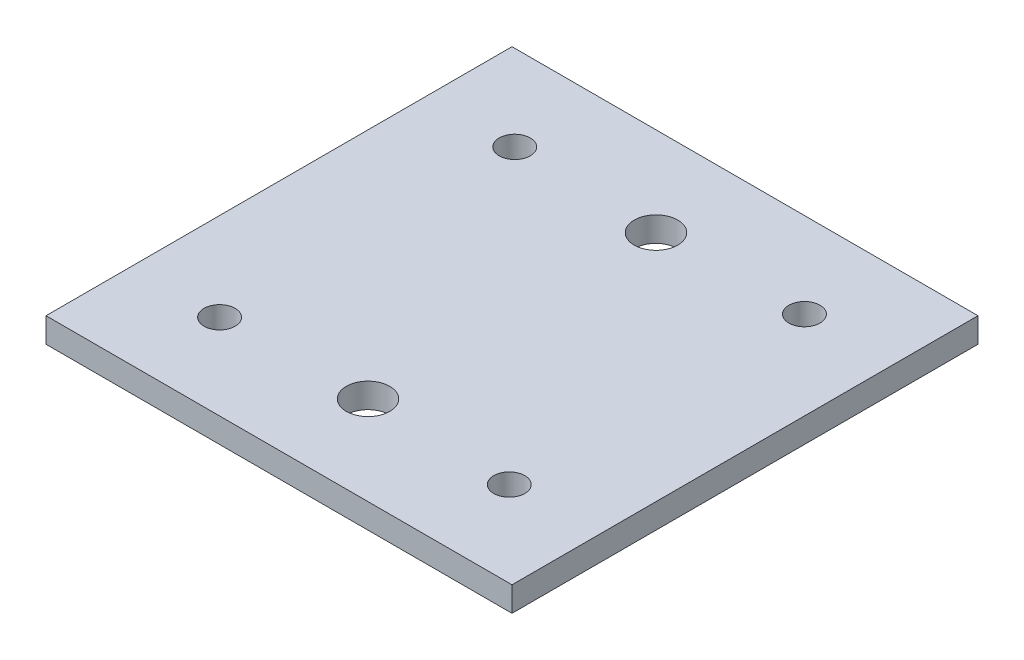
SolidWorks part; units mm, degrees
ref_plane "Front Plane" through (0, 0, 0) normal (0, 0, 1) x (1, 0, 0)
ref_plane "Top Plane" through (0, 0, 0) normal (0, 1, 0) x (1, 0, 0)
ref_plane "Right Plane" through (0, 0, 0) normal (1, 0, 0) x (0, 0, -1)
sketch "Sketch1" plane through (0, 0, 0) normal (1, 0, 0) x (0, 0, -1)
  line L1 (0, 0) -> (150, 0)
  line L2 (0, 0) -> (0, -7.9622)
  line L3 (0, -7.9622) -> (150, -7.9622)
  line L4 (150, 0) -> (150, -7.9622)
  dimension "D1" = 150
extrude "Boss-Extrude1" add sketch "Sketch1" along normal blind 150 contours L3 L4 L1 L2
sketch "Sketch2" plane through (0, 0, 0) normal (0, 1, 0) x (1, 0, 0)
  line L0 (75, 150) -> (75, 0) construction
  line L1 (150, 150) -> (0, 150) construction
  line L2 (150, 0) -> (0, 0) construction
  line L3 (150, 75) -> (0, 75) construction
  line L4 (150, 0) -> (150, 150) construction
  line L5 (0, 0) -> (0, 150) construction
  circle A0 centre (74.9999, 121.3474) radius 7
  circle A2 centre (75.0001, 121.3474) radius 7
  circle A3 centre (74.9999, 28.6526) radius 7
  point P12 (75, 75)
  dimension "D1" = 14
  dimension "D2" = 46.3474
sketch "Sketch3" plane through (0, -7.9622, 0) normal (0, -1, 0) x (1, 0, 0)
  line L0 (75, -150) -> (75, 0) construction
  line L1 (150, -150) -> (0, -150) construction
  line L2 (150, 0) -> (0, 0) construction
  line L3 (0, -75) -> (150, -75) construction
  line L4 (0, 0) -> (0, -150) construction
  line L5 (150, 0) -> (150, -150) construction
  circle A1 centre (28.3715, -122.5) radius 5
  circle A2 centre (28.3715, -27.5) radius 5
  circle A3 centre (121.6285, -27.5) radius 5
  circle A4 centre (121.6285, -122.5) radius 5
  dimension "D1" = 10
  dimension "D2" = 47.5
extrude "Cut-Extrude1" cut sketch "Sketch2" against normal through all contours A0 | A3
extrude "Cut-Extrude2" cut sketch "Sketch3" against normal through all
